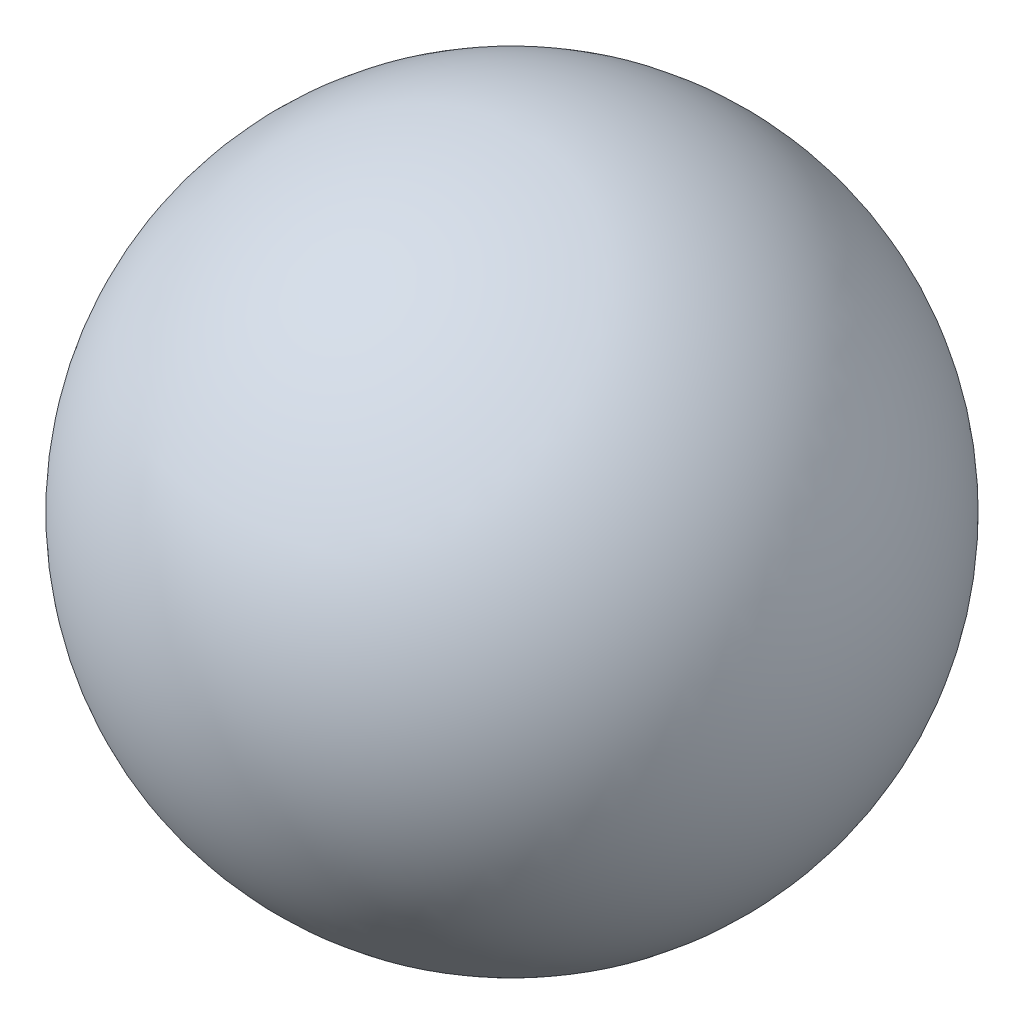
SolidWorks part; units mm, degrees
ref_plane "Front Plane" through (0, 0, 0) normal (0, 0, 1) x (1, 0, 0)
ref_plane "Top Plane" through (0, 0, 0) normal (0, 1, 0) x (1, 0, 0)
ref_plane "Right Plane" through (0, 0, 0) normal (1, 0, 0) x (0, 0, -1)
sketch "Sketch2" plane through (0, 0, 0) normal (0, 0, 1) x (1, 0, 0)
  line L0 (0, -158.4863) -> (0, 158.4863) construction
  line L1 (0, 19.05) -> (0, 18.5674)
  line L2 (0, -18.5674) -> (0, -19.05)
  arc A0 (0, -19.05) -> (0, 19.05) centre (0, 0) ccw
  arc A1 (0, -18.5674) -> (0, 18.5674) centre (0, 0) ccw
  circle A2 centre (0, 0) radius 19.05 construction
  circle A3 centre (0, 0) radius 18.5674 construction
  point P4 (0, 0)
  dimension "D2" = 19.05
  dimension "D1" = 0.4826
revolve "Revolve1" add sketch "Sketch2" angle 360 about L0
